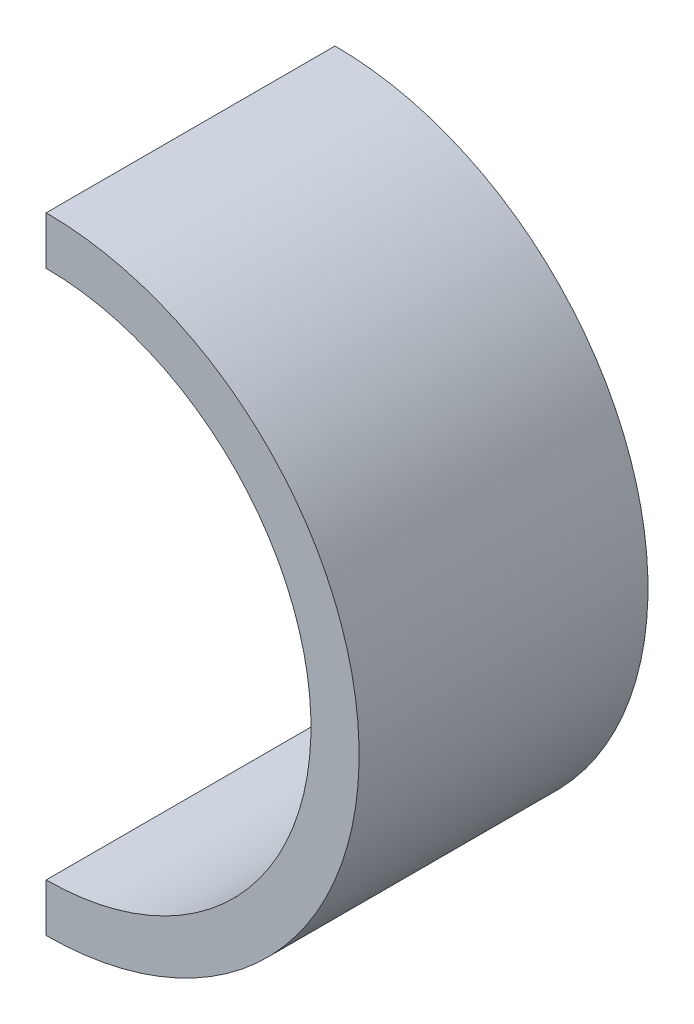
SolidWorks part; units mm, degrees
ref_plane "Front Plane" through (0, 0, 0) normal (0, 0, 1) x (1, 0, 0)
ref_plane "Top Plane" through (0, 0, 0) normal (0, 1, 0) x (1, 0, 0)
ref_plane "Right Plane" through (0, 0, 0) normal (1, 0, 0) x (0, 0, -1)
sketch "Sketch2" plane through (0, 0, 0) normal (0, 0, 1) x (1, 0, 0)
  line L2 (0, -32.5) -> (0, 32.5) construction
  line L3 (0, 32.5) -> (0, 27.5)
  line L4 (0, -32.5) -> (0, -27.5)
  arc A2 (0, -32.5) -> (0, 32.5) centre (0, 0) ccw
  arc A3 (0, -27.5) -> (0, 27.5) centre (0, 0) ccw
  point P3 (0, 0)
  point P4 (0, 0)
  dimension "D2" = 55
  dimension "D1" = 65
extrude "Boss-Extrude1" add sketch "Sketch2" along normal blind 30
